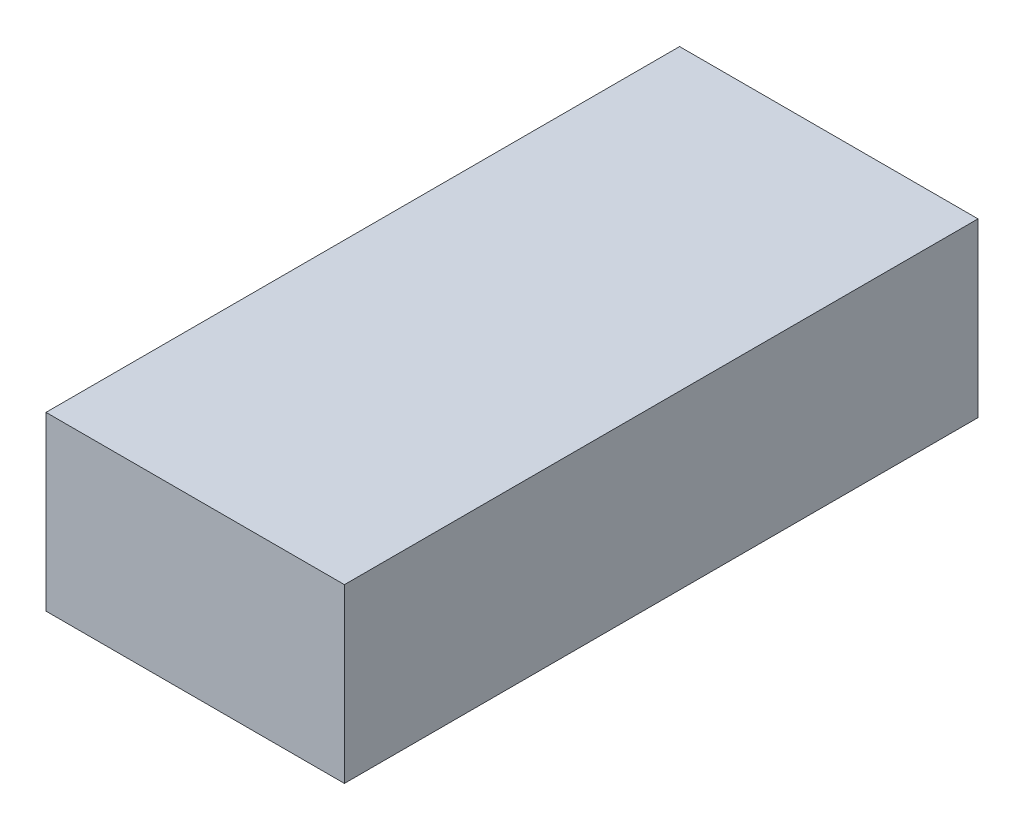
SolidWorks part; units mm, degrees
ref_plane "Front Plane" through (0, 0, 0) normal (0, 0, 1) x (1, 0, 0)
ref_plane "Top Plane" through (0, 0, 0) normal (0, 1, 0) x (1, 0, 0)
ref_plane "Right Plane" through (0, 0, 0) normal (1, 0, 0) x (0, 0, -1)
sketch "Sketch1" plane through (0, 0, 0) normal (0, 1, 0) x (1, 0, 0)
  line L1 (0, 0) -> (33.02, 0)
  line L2 (0, 0) -> (0, 70.104)
  line L3 (0, 70.104) -> (33.02, 70.104)
  line L4 (33.02, 0) -> (33.02, 70.104)
  dimension "D1" = 33.02
  dimension "D2" = 70.104
extrude "Boss-Extrude1" add sketch "Sketch1" along normal blind 19.05
